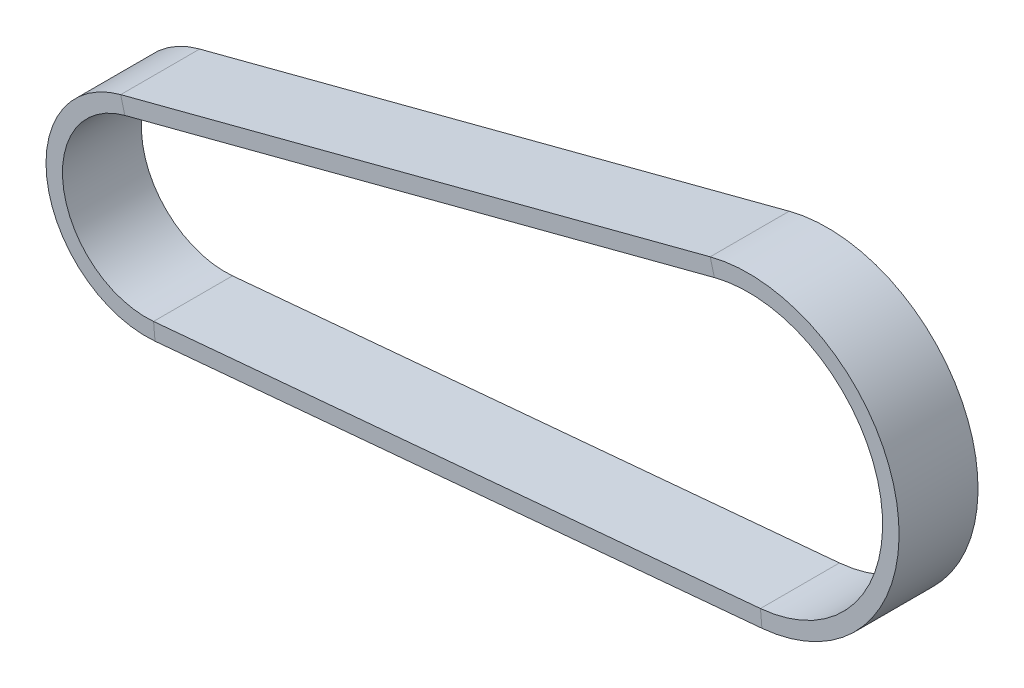
SolidWorks part; units mm, degrees
material "POLYURETHANE (11671)"
ref_plane "Front Plane" through (0, 0, 0) normal (0, 0, 1) x (1, 0, 0)
ref_plane "Top Plane" through (0, 0, 0) normal (0, 1, 0) x (1, 0, 0)
ref_plane "Right Plane" through (0, 0, 0) normal (1, 0, 0) x (0, 0, -1)
sketch "Sketch1" plane through (0, 0, 0) normal (0, 0, 1) x (1, 0, 0)
  circle A2 centre (-45.7667, -8) radius 6.35
  circle A3 centre (0, 0) radius 10.2
  point P6 (0, 0)
  point P7 (0, 0)
sketch "Sketch2" plane through (0, 0, 0) normal (0, 0, 1) x (1, 0, 0)
  line L0 (0.9177, -10.1586) -> (-45.1954, -14.3242)
  line L1 (-2.5829, 9.8676) -> (-47.3747, -1.857)
  circle A0 centre (-45.7667, -8) radius 6.35 construction
  circle A1 centre (0, 0) radius 10.2 construction
  arc A2 (-47.3747, -1.857) -> (-45.1954, -14.3242) centre (-45.7667, -8) ccw
  arc A3 (0.9177, -10.1586) -> (-2.5829, 9.8676) centre (0, 0) ccw
ref_plane "Plane1" through (0.9177, -10.1586, 0) normal (-0.9959, -0.09, 0) x (0, 0, 1)
sketch "Sketch3" plane through (0.9177, -10.1586, 0) normal (-0.9959, -0.09, 0) x (0, 0, 1)
  line L0 (3, -1.25) -> (3, 0)
  line L1 (3, -1.25) -> (-3, -1.25)
  line L2 (3, 0) -> (-3, 0)
  line L3 (-3, -1.25) -> (-3, 0)
  line L4 (3, -1.25) -> (-3, 0) construction
  line L5 (3, 0) -> (-3, -1.25) construction
  point P0 (0, 0)
  point P1 (0, -0.625)
  dimension "D1" = 6
  dimension "D2" = 1.25
sweep "Sweep1" add profiles "Sketch3" path "Sketch2"
